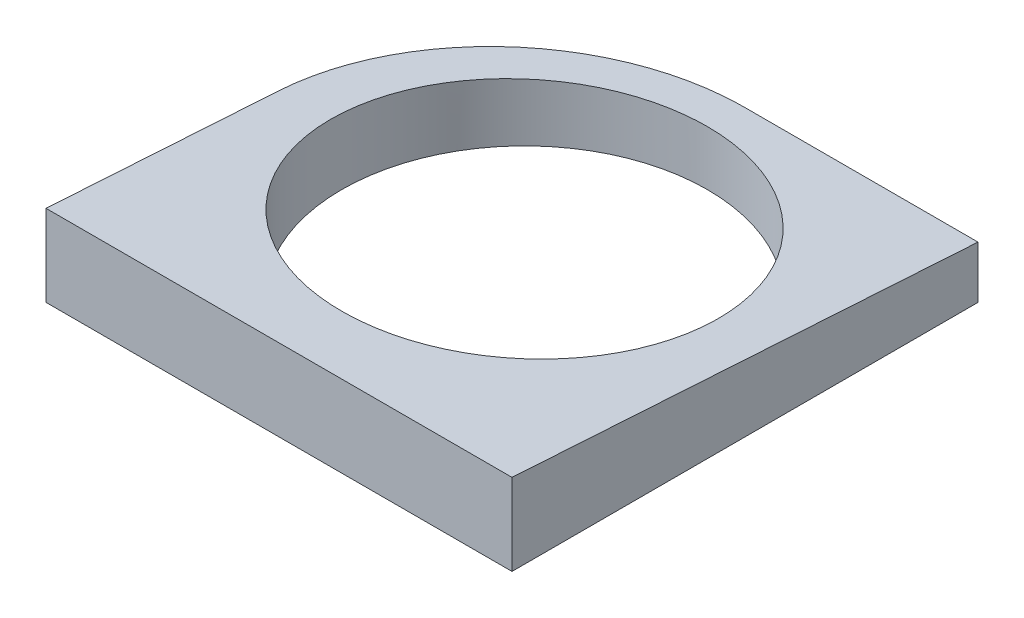
SolidWorks part; units mm, degrees
ref_plane "Front Plane" through (0, 0, 0) normal (0, 0, 1) x (1, 0, 0)
ref_plane "Top Plane" through (0, 0, 0) normal (0, 1, 0) x (1, 0, 0)
ref_plane "Right Plane" through (0, 0, 0) normal (1, 0, 0) x (0, 0, -1)
sketch "Sketch1" plane through (0, 0, 0) normal (0, 1, 0) x (1, 0, 0)
  line L0 (0, -60.1358) -> (0, 92.921) construction
  line L1 (-22.3, -23.5) -> (22.3, -23.5)
  line L2 (22.3, -23.5) -> (22.3, 21.1)
  line L3 (22.3, 21.1) -> (0, 21.1)
  line L4 (-22.3, -1.2) -> (-22.3, -23.5)
  arc A0 (0, 21.1) -> (-22.3, -1.2) centre (0, -1.2) ccw
  circle A1 centre (0, 0) radius 17.5
  point P7 (0, -23.5)
  point P8 (0, -17.5)
  point P9 (0, 17.5)
  point P10 (0, 21.1)
  dimension "D1" = 35
  dimension "D2" = 6
  dimension "D3" = 3.6
extrude "Boss-Extrude1" add sketch "Sketch1" along normal blind 300
sketch "Sketch2" plane through (0, 0, 0) normal (1, 0, 0) x (0, 0, -1)
  line L1 (-23.5, 7.8) -> (21.1, 5)
  line L5 (-23.5, 331.9393) -> (89.8957, 331.9393)
  line L6 (-23.5, 331.9393) -> (-23.5, 7.8)
  line L7 (21.1, 5) -> (89.8957, 5)
  line L8 (89.8957, 331.9393) -> (89.8957, 5)
  line L10 (-1.2, 0) -> (21.1, 0) construction
  line L11 (-23.5, 300) -> (-23.5, 0) construction
  line L12 (21.1, 300) -> (21.1, 0) construction
  dimension "D1" = 5
  dimension "D2" = 2.8
extrude "Cut-Extrude1" cut sketch "Sketch2" against normal mid plane 300
